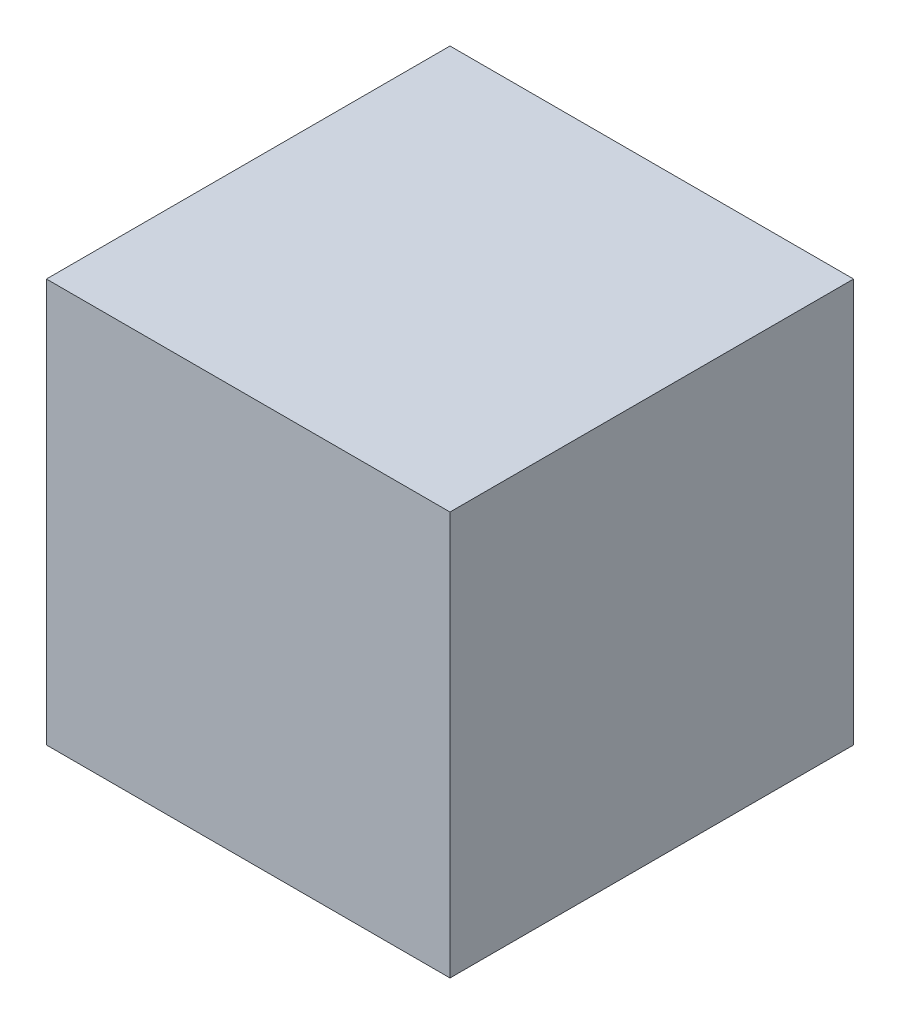
SolidWorks part; units mm, degrees
ref_plane "Front Plane" through (0, 0, 0) normal (0, 0, 1) x (1, 0, 0)
ref_plane "Top Plane" through (0, 0, 0) normal (0, 1, 0) x (1, 0, 0)
ref_plane "Right Plane" through (0, 0, 0) normal (1, 0, 0) x (0, 0, -1)
sketch "Sketch1" plane through (0, 0, 0) normal (0, 0, 1) x (1, 0, 0)
  line L1 (-127, -127) -> (127, -127)
  line L2 (-127, -127) -> (-127, 127)
  line L3 (-127, 127) -> (127, 127)
  line L4 (127, -127) -> (127, 127)
  line L5 (-127, -127) -> (127, 127) construction
  line L6 (-127, 127) -> (127, -127) construction
  point P0 (0, 0)
  dimension "D1" = 254
extrude "Boss-Extrude1" add sketch "Sketch1" along normal mid plane 254
sketch "Sketch2" plane through (0, 0, 127) normal (0, 0, 1) x (1, 0, 0)
  line L8 (124.46, -124.46) -> (124.46, 124.46)
  line L9 (124.46, 124.46) -> (-124.46, 124.46)
  line L10 (-124.46, 124.46) -> (-124.46, -124.46)
  line L11 (-124.46, -124.46) -> (124.46, -124.46)
  line L12 (124.46, -124.46) -> (124.46, 124.46)
  line L13 (124.46, 124.46) -> (-124.46, 124.46)
  line L14 (-124.46, 124.46) -> (-124.46, -124.46)
  line L15 (-124.46, -124.46) -> (124.46, -124.46)
  dimension "D1" = 2.54
equation "\"side_length\"= 10"
equation "\"D1@Sketch1\"=\"side_length\""
equation "\"D1@Boss-Extrude1\"=\"side_length\""
equation "\"recess\"=0.1"
equation "\"D1@Sketch2\"=\"recess\""
